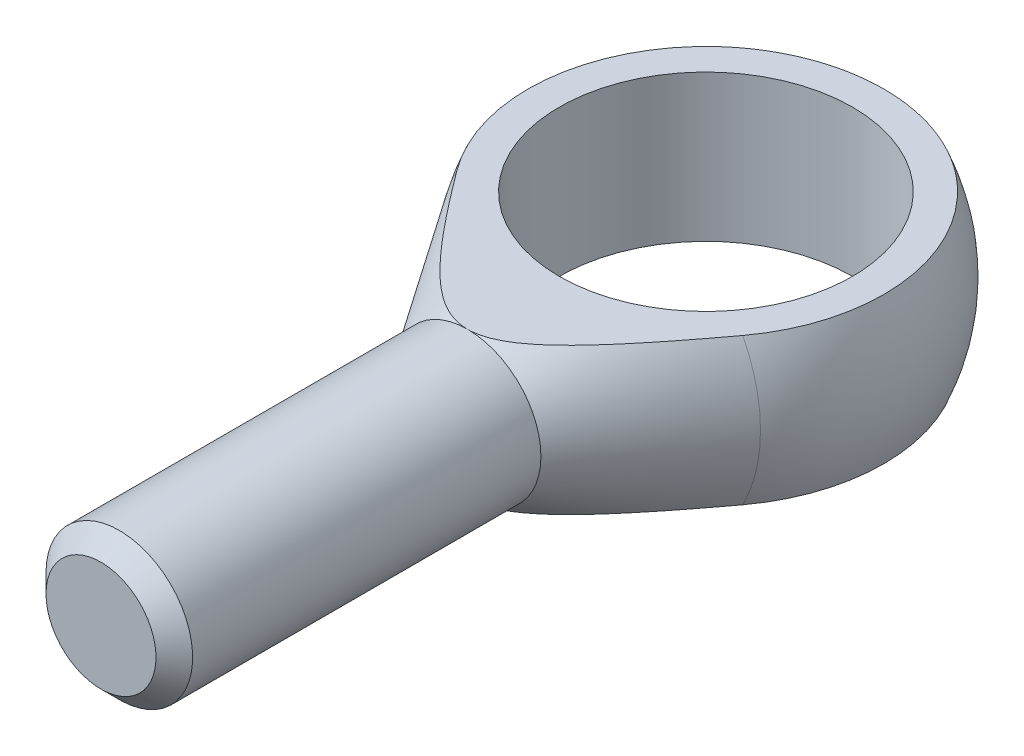
SolidWorks part; units mm, degrees
material "1.0545 (S355N)"
ref_plane "Płaszczyzna przednia" through (0, 0, 0) normal (0, 0, 1) x (1, 0, 0)
ref_plane "Płaszczyzna górna" through (0, 0, 0) normal (0, 1, 0) x (1, 0, 0)
ref_plane "Płaszczyzna prawa" through (0, 0, 0) normal (1, 0, 0) x (0, 0, -1)
sketch "Szkic1" plane through (0, 0, 0) normal (0, 1, 0) x (1, 0, 0)
  line L0 (0, 26.0435) -> (0, -71.4286) construction
  line L1 (-8, -66) -> (8, -66)
  line L2 (8, -66) -> (8, -26)
  line L3 (-8, -66) -> (-8, -26)
  line L4 (-17.526, -11.5689) -> (-8, -26)
  line L5 (8, -26) -> (17.526, -11.5689)
  line L6 (-8, -26) -> (8, -26)
  line L7 (0, 21) -> (0, -66)
  arc A0 (17.526, -11.5689) -> (-17.526, -11.5689) centre (0, 0) ccw
  point P7 (0, -66)
  dimension "d4" = 42
  dimension "d2" = 16
  dimension "l1" = 66
  dimension "l3" = 40
revolve "Obrót1" add sketch "Szkic1" angle 360 about L0
sketch "Szkic2" plane through (0, 0, 0) normal (1, 0, 0) x (0, 0, -1)
  line L4 (-26, 8) -> (19.4165, 8)
  line L5 (-26, -8) -> (19.4165, -8)
  line L6 (-26, -8) -> (-11.5689, -17.526) construction
  line L7 (-11.5689, 17.526) -> (-26, 8) construction
  line L8 (-26, -8) -> (-11.5689, -17.526)
  line L9 (-11.5689, 17.526) -> (-26, 8)
  arc A0 (-11.5689, -17.526) -> (-11.5689, 17.526) centre (0, 0) ccw construction
  arc A1 (-11.5689, -17.526) -> (19.4165, -8) centre (0, 0) ccw
  arc A2 (19.4165, 8) -> (-11.5689, 17.526) centre (0, 0) ccw
extrude "Wytnij-wyciągnięcie1" cut sketch "Szkic2" against normal through all both and the other way through all
sketch "Szkic3" plane through (0, 0, 0) normal (0, 1, 0) x (1, 0, 0)
  circle A0 centre (0, 0) radius 16
  dimension "b" = 32
extrude "Wytnij-wyciągnięcie2" cut sketch "Szkic3" against normal through all both and the other way through all contours A0
chamfer "Sfazowanie1" distance 2 angle 45 1 edges at (-8, 0, 66)
equation "\"D1@Sfazowanie1\"=\"l3@Szkic1\"*0.05"
